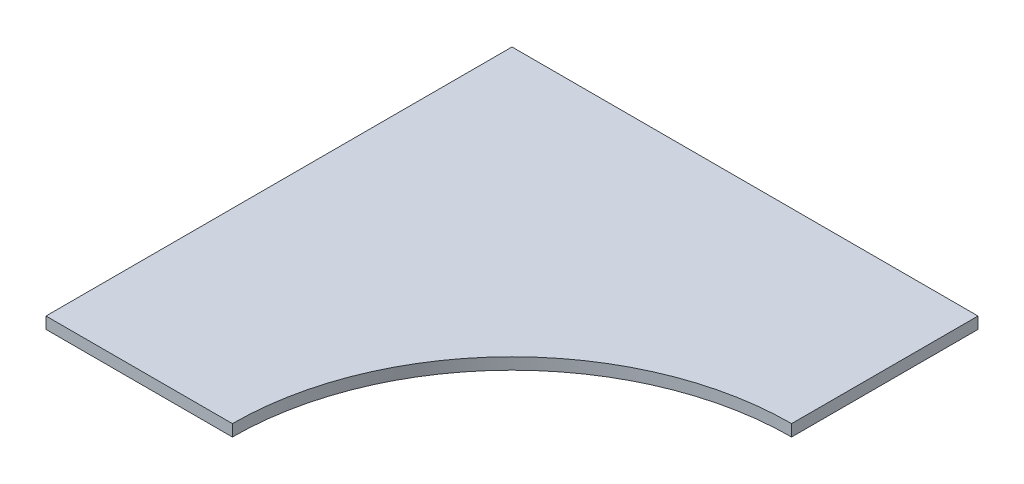
SolidWorks part; units mm, degrees
material "6061-T6 (SS)"
ref_plane "Front Plane" through (0, 0, 0) normal (0, 0, 1) x (1, 0, 0)
ref_plane "Top Plane" through (0, 0, 0) normal (0, 1, 0) x (1, 0, 0)
ref_plane "Right Plane" through (0, 0, 0) normal (1, 0, 0) x (0, 0, -1)
sketch "Sketch1" plane through (0, 0, 0) normal (0, 1, 0) x (1, 0, 0)
  line L0 (0, 0) -> (0, 127)
  line L1 (0, 127) -> (127, 127)
  line L2 (127, 127) -> (127, 76.2)
  line L3 (0, 0) -> (50.8, 0)
  arc A0 (50.8, 0) -> (127, 76.2) centre (127, 0) cw
  dimension "D1" = 127
  dimension "D2" = 127
  dimension "D3" = 50.8
  dimension "D4" = 50.8
extrude "Boss-Extrude1" add sketch "Sketch1" along normal blind 3.175
